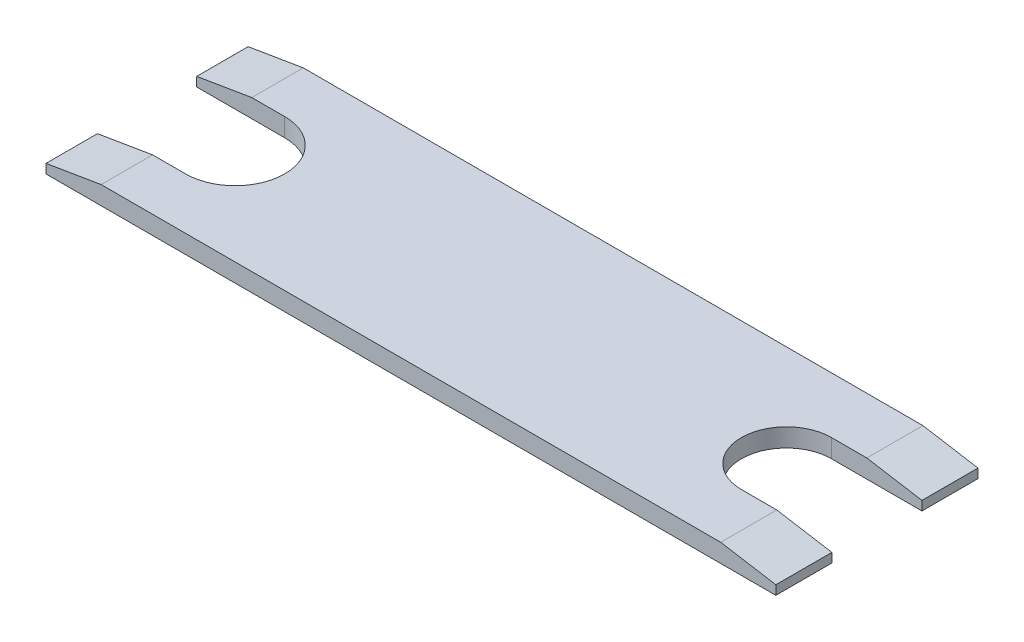
SolidWorks part; units mm, degrees
ref_plane "Front Plane" through (0, 0, 0) normal (0, 0, 1) x (1, 0, 0)
ref_plane "Top Plane" through (0, 0, 0) normal (0, 1, 0) x (1, 0, 0)
ref_plane "Right Plane" through (0, 0, 0) normal (1, 0, 0) x (0, 0, -1)
sketch "Sketch1" plane through (0, 0, 0) normal (0, 1, 0) x (1, 0, 0)
  line L0 (15, 0) -> (-15, 0) construction
  line L1 (-15, 0) -> (15, 0) construction
  line L2 (-15, 5.5) -> (15, 5.5)
  line L3 (-15, -5.5) -> (15, -5.5)
  circle A0 centre (-15, 0) radius 2.7
  circle A1 centre (15, 0) radius 2.45
  arc A2 (-15, 5.5) -> (-15, -5.5) centre (-15, 0) ccw
  arc A3 (15, -5.5) -> (15, 5.5) centre (15, 0) ccw
  point P4 (0, 0)
  point P7 (0, 0)
  dimension "D1" = 4.9
  dimension "D2" = 5.4
  dimension "D4" = 5.5
  dimension "D3" = 30
extrude "Boss-Extrude1" add sketch "Sketch1" along normal blind 1
sketch "Sketch2" plane through (0, 1, 0) normal (0, 1, 0) x (1, 0, 0)
  line L1 (-15, 2.7) -> (-20.5, 2.7)
  line L2 (-15, 2.7) -> (-15, -2.7)
  line L3 (-15, -2.7) -> (-20.5, -2.7)
  line L4 (-20.5, 2.7) -> (-20.5, -2.7)
  line L5 (-17.75, -2.7) -> (-17.75, 2.7) construction
  line L6 (-15, 0) -> (-20.5, 0) construction
  line L7 (15, 2.45) -> (20.5, 2.45)
  line L8 (15, 2.45) -> (15, -2.45)
  line L9 (15, -2.45) -> (20.5, -2.45)
  line L10 (20.5, 2.45) -> (20.5, -2.45)
  line L11 (17.75, -2.45) -> (17.75, 2.45) construction
  line L12 (15, 0) -> (20.5, 0) construction
  circle A0 centre (-15, 0) radius 2.7 construction
  circle A1 centre (15, 0) radius 2.45 construction
  arc A2 (-15, 5.5) -> (-15, -5.5) centre (-15, 0) ccw construction
  arc A3 (15, -5.5) -> (15, 5.5) centre (15, 0) ccw construction
  point P12 (11.1421, -2.45)
  point P13 (-11.1421, -2.7)
  point P14 (-15.3334, 0)
  point P18 (15.3334, 0)
  point P22 (11.1421, 2.45)
  point P23 (0, 0)
  point P24 (0, 0)
  point P200 (-17.75, 0)
  point P243 (17.75, 0)
extrude "Cut-Extrude1" cut sketch "Sketch2" against normal through all
sketch "Sketch3" plane through (0, 0, 0) normal (0, -1, 0) x (1, 0, 0)
  line L0 (-19.7917, 2.7) -> (-19.7917, 5.5)
  line L1 (-19.7917, 5.5) -> (-15, 5.5)
  line L2 (15, 5.5) -> (19.9242, 5.5)
  line L3 (19.9242, 5.5) -> (19.9242, 2.45)
  line L4 (19.9242, -2.45) -> (19.9242, -5.5)
  line L5 (19.9242, -5.5) -> (15, -5.5)
  line L6 (-19.7917, 2.7) -> (-15, 2.7)
  line L7 (-15, -2.7) -> (-19.7917, -2.7)
  line L8 (-15, -5.5) -> (15, -5.5)
  line L9 (19.9242, -2.45) -> (15, -2.45)
  line L10 (15, 2.45) -> (19.9242, 2.45)
  line L11 (15, 5.5) -> (-15, 5.5)
  line L18 (-15, -5.5) -> (-19.7917, -5.5)
  line L19 (-19.7917, -5.5) -> (-19.7917, -2.7)
  arc A6 (-15, 5.5) -> (-19.7917, 2.7) centre (-15, 0) ccw
  arc A7 (-15, -2.7) -> (-15, 2.7) centre (-15, 0) ccw
  arc A8 (-19.7917, -2.7) -> (-15, -5.5) centre (-15, 0) ccw
  arc A9 (15, -5.5) -> (19.9242, -2.45) centre (15, 0) ccw
  arc A10 (15, 2.45) -> (15, -2.45) centre (15, 0) ccw
  arc A11 (19.9242, 2.45) -> (15, 5.5) centre (15, 0) ccw
  arc A12 (-15, 5.5) -> (-19.7917, 2.7) centre (-15, 0) ccw
  arc A14 (-19.7917, -2.7) -> (-15, -5.5) centre (-15, 0) ccw
  arc A15 (15, -5.5) -> (19.9242, -2.45) centre (15, 0) ccw
  arc A17 (19.9242, 2.45) -> (15, 5.5) centre (15, 0) ccw
  dimension "D1" = 0
extrude "Boss-Extrude2" add sketch "Sketch3" against normal up to surface (1 mm away) up to face at (0.0521, 1, 0)
chamfer "Chamfer1" distance 3 distance2 0.5 4 edges at (19.9242, 1, 3.975) (19.9242, 1, -3.975) (-19.7917, 1, -4.1) (-19.7917, 1, 4.1)
